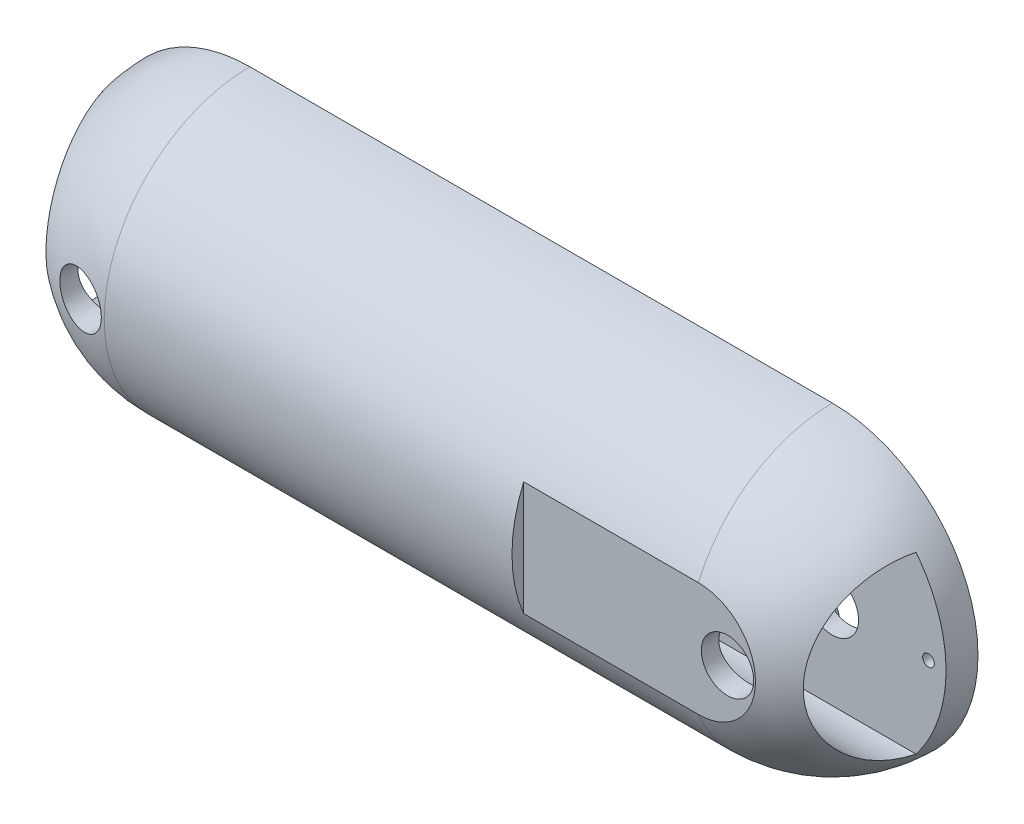
SolidWorks part; units mm, degrees
ref_plane "Ebene vorne" through (0, 0, 0) normal (0, 0, 1) x (1, 0, 0)
ref_plane "Ebene oben" through (0, 0, 0) normal (0, 1, 0) x (1, 0, 0)
ref_plane "Ebene rechts" through (0, 0, 0) normal (1, 0, 0) x (0, 0, -1)
sketch "Sketch5" plane through (0, 0, 0) normal (0, 0, 1) x (1, 0, 0)
  line L0 (-64.6766, 0) -> (63.3831, 0) construction
  line L1 (0, 0) -> (-100, 0)
  line L3 (-100, 25) -> (0, 25)
  line L5 (-100, 0) -> (-125, 0)
  line L6 (0, 0) -> (25, 0)
  arc A0 (-100, 25) -> (-125, 0) centre (-100, 0) ccw
  arc A1 (25, 0) -> (0, 25) centre (0, 0) ccw
  dimension "D2" = 150
  dimension "D1" = 25
revolve "Revolve1" add sketch "Sketch5" angle 180 about L0
sketch "Sketch7" plane through (0, 0, 0) normal (0, 0, -1) x (-1, 0, 0)
  circle A0 centre (-5, 0) radius 4.5
  circle A1 centre (105, 0) radius 4.5
  arc A4 (0, 25) -> (0, -25) centre (0, 0) ccw construction
  arc A5 (100, -25) -> (100, 25) centre (100, 0) ccw construction
  point P7 (-25, 0)
  point P16 (125, 0)
  dimension "D1" = 9
  dimension "D2" = 20
  dimension "D3" = 20
  dimension "D4" = 2
extrude "Cut-Extrude2" cut sketch "Sketch7" against normal through all
sketch "Sketch10" plane through (0, 0, 0) normal (1, 0, 0) x (0, 0, -1)
  line L0 (-5, 15) -> (-5, -15)
  line L1 (0, -25) -> (0, 25) construction
  arc A0 (-5, 15) -> (-5, -15) centre (-5, 0) ccw
  arc A1 (0, 25) -> (0, -25) centre (0, 0) ccw construction
  point P5 (-20, 0)
  point P10 (-25, 0)
  dimension "D1" = 5
  dimension "D2" = 5
extrude "Cut-Extrude5" cut sketch "Sketch10" against normal through all both and the other way through all
sketch "Sketch12" plane through (0, 0, 0) normal (1, 0, 0) x (0, 0, -1)
  line L0 (0, -25) -> (0, 25) construction
  line L1 (-28, 25) -> (-23, 25)
  line L2 (-28, 25) -> (-28, -25)
  line L3 (-28, -25) -> (-23, -25)
  line L4 (-23, 25) -> (-23, -25)
  dimension "D1" = 50
  dimension "D2" = 5
  dimension "D3" = 23
extrude "Cut-Extrude6" cut sketch "Sketch12" against normal blind 30 and the other way blind 20
sketch "Sketch13" plane through (0, 0, 5) normal (0, 0, 1) x (1, 0, 0)
  line L0 (0.4038, -4.5962) -> (9.5962, 4.5962) construction
  line L3 (19, 0) -> (-9, 0) construction
  line L4 (5, 19) -> (5, -19) construction
  line L5 (5, 4.5) -> (5, -4.5) construction
  line L6 (0.4038, 4.5962) -> (9.5962, -4.5962) construction
  line L7 (7.5, 16.5) -> (8.7918, 6.456)
  line L8 (2.5, 16.5) -> (1.0961, 6.3439)
  line L9 (-11.5, 2.5) -> (-1.456, 3.7918)
  line L10 (-11.5, -2.5) -> (-1.3439, -3.9039)
  line L11 (2.5, -16.5) -> (1.2082, -6.456)
  line L12 (7.5, -16.5) -> (8.9039, -6.3439)
  line L13 (21.5, -2.5) -> (11.456, -3.7918)
  line L14 (-109.5962, -4.5962) -> (-100.4038, 4.5962) construction
  line L15 (-86, 0) -> (-124, 0) construction
  line L16 (-105, 19) -> (-105, -19) construction
  line L17 (-105, 5.0958) -> (-105, -5.0958) construction
  line L18 (-109.5962, 4.5962) -> (-100.4038, -4.5962) construction
  line L26 (-102.5, 16.5) -> (-101.1275, 6.4039)
  line L27 (-107.5, 16.5) -> (-108.8231, 6.4039)
  line L28 (-121.5, 2.5) -> (-111.3231, 3.9039)
  line L29 (-121.5, -2.5) -> (-111.3231, -3.7918)
  line L30 (-107.5, -16.5) -> (-108.8231, -6.2918)
  line L31 (-102.5, -16.5) -> (-101.1275, -6.2918)
  line L32 (-88.5, -2.5) -> (-98.6275, -3.7918)
  arc A2 (7.5, 16.5) -> (2.5, 16.5) centre (5, 16.5) ccw
  arc A3 (-1.456, 3.7918) -> (1.0961, 6.3439) centre (-1.456, 6.3439) ccw
  arc A4 (21.5, -2.5) -> (21.5, 2.5) centre (21.5, 0) ccw
  circle A5 centre (5, 0) radius 4.5 construction
  arc A6 (2.5, -16.5) -> (7.5, -16.5) centre (5, -16.5) ccw
  arc A7 (-11.5, 2.5) -> (-11.5, -2.5) centre (-11.5, 0) ccw
  arc A8 (8.7918, 6.456) -> (11.3439, 3.9039) centre (11.3439, 6.456) ccw
  arc A9 (11.456, -3.7918) -> (8.9039, -6.3439) centre (11.456, -6.3439) ccw
  arc A10 (1.2082, -6.456) -> (-1.3439, -3.9039) centre (-1.3439, -6.456) ccw
  arc A19 (-102.5, 16.5) -> (-107.5, 16.5) centre (-105, 16.5) ccw
  arc A20 (-111.3231, 3.9039) -> (-108.8231, 6.4039) centre (-111.3231, 6.4039) ccw
  arc A21 (-88.5, -2.5) -> (-88.5, 2.5) centre (-88.5, 0) ccw
  arc A22 (-107.5, -16.5) -> (-102.5, -16.5) centre (-105, -16.5) ccw
  arc A23 (-121.5, 2.5) -> (-121.5, -2.5) centre (-121.5, 0) ccw
  arc A24 (-101.1275, 6.4039) -> (-98.6275, 3.9039) centre (-98.6275, 6.4039) ccw
  arc A25 (-98.6275, -3.7918) -> (-101.1275, -6.2918) centre (-98.6275, -6.2918) ccw
  arc A26 (-108.8231, -6.2918) -> (-111.3231, -3.7918) centre (-111.3231, -6.2918) ccw
  spline S0 degree 1 poles (21.5, 2.5) (11.3439, 3.9039) knots 0 0 1 1
  spline S1 degree 1 poles (-88.5, 2.5) (-98.6275, 3.9039) knots 0 0 1 1
  point P0 (5, 0)
  point P3 (5, 0)
  point P6 (5, 0)
  point P7 (24, 0)
  point P8 (5, 0)
  point P12 (5, 0)
  point P22 (-105, 0)
  point P31 (-105, 0)
  point P32 (5, 0)
  point P38 (-105, 0)
  point P39 (5, 0)
  point P55 (-105, 0)
  point P59 (-105, 0)
  point P75 (-200.8042, 13.8568)
  dimension "D1" = 19
  dimension "D7" = 5
  dimension "D2" = 45
  dimension "D13" = 5
  dimension "D16" = 2.5
  dimension "D20" = 2.5
  dimension "D21" = 2.5
  dimension "D22" = 2.5
  dimension "D23" = 2.5
  dimension "D17" = 2.5
  dimension "D3" = 45
  dimension "D4" = 13
  dimension "D5" = 45
  dimension "D6" = 13
  dimension "D10" = 13
  dimension "D11" = 45
  dimension "D12" = 13
  dimension "D14" = 38
  dimension "D15" = 38
  dimension "D18" = 7.6956
  dimension "D19" = 7.6956
  dimension "D8" = 4
  dimension "D9" = 4
extrude "Cut-Extrude7" cut sketch "Sketch13" along normal blind 2 from offset 5 offset against normal yes
sketch "Sketch14" plane through (0, 0, 2) normal (0, 0, -1) x (-1, 0, 0)
  circle A6 centre (-5, 16.5) radius 1
  circle A7 centre (11.5, 0) radius 1
  circle A8 centre (-5, -16.5) radius 1
  circle A9 centre (-21.5, 0) radius 1
  circle A10 centre (105, 16.5) radius 1
  circle A15 centre (121.5, 0) radius 1
  circle A16 centre (105, -16.5) radius 1
  circle A17 centre (88.5, 0) radius 1
  point P15 (-5, 0)
  point P32 (105, 0)
  point P33 (105, 0)
  dimension "D1" = 2
  dimension "D3" = 2
  dimension "D2" = 16.5
  dimension "D4" = 16.5
extrude "Cut-Extrude8" cut sketch "Sketch14" against normal blind 5
